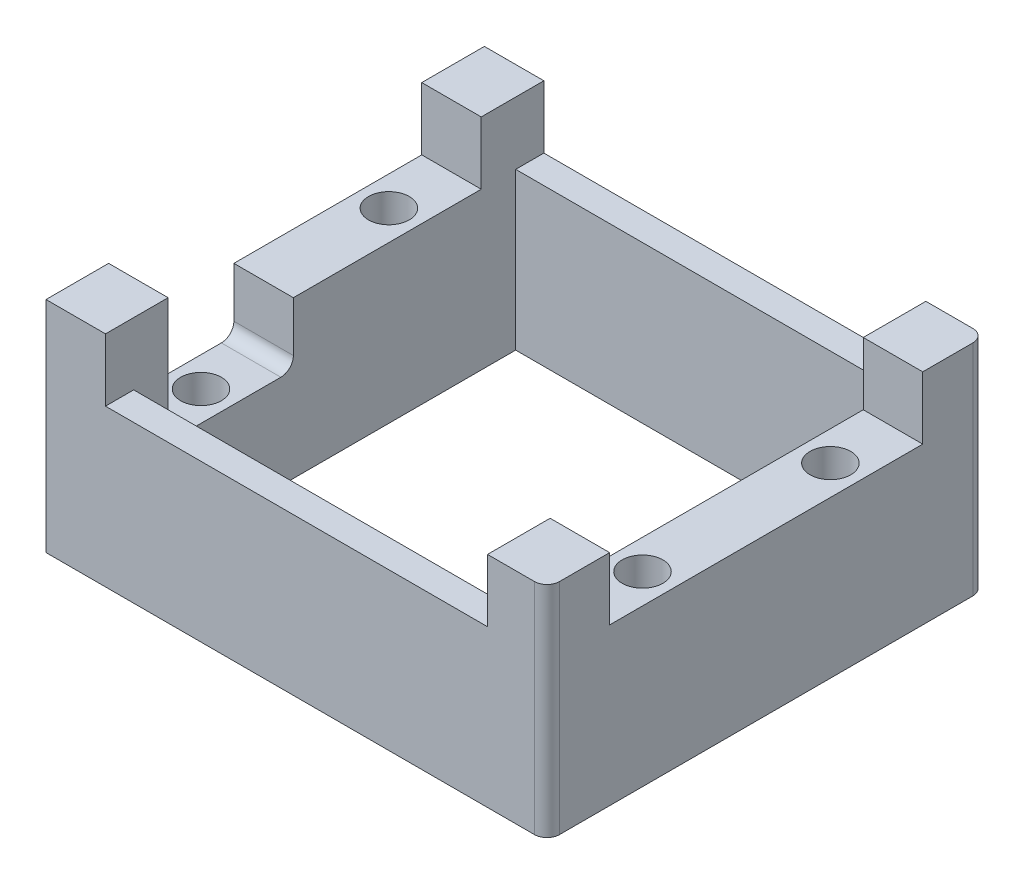
SolidWorks part; units mm, degrees
ref_plane "Front Plane" through (0, 0, 0) normal (0, 0, 1) x (1, 0, 0)
ref_plane "Top Plane" through (0, 0, 0) normal (0, 1, 0) x (1, 0, 0)
ref_plane "Right Plane" through (0, 0, 0) normal (1, 0, 0) x (0, 0, -1)
sketch "Sketch1" plane through (0, 0, 0) normal (0, 1, 0) x (1, 0, 0)
  line L1 (-35.2325, 39.1878) -> (44.7675, 39.1878)
  line L2 (-35.2325, 39.1878) -> (-35.2325, -30.8122)
  line L3 (-35.2325, -30.8122) -> (44.7675, -30.8122)
  line L4 (44.7675, 39.1878) -> (44.7675, -30.8122)
  dimension "D1" = 70
  dimension "D2" = 80
extrude "Boss-Extrude1" add sketch "Sketch1" along normal blind 25
sketch "Sketch2" plane through (0, 25, 0) normal (0, 1, 0) x (1, 0, 0)
  line L0 (-35.2325, 39.1878) -> (-35.2325, -30.8122) construction
  line L1 (-25.7325, 34.6878) -> (35.2675, 34.6878)
  line L2 (-25.7325, 34.6878) -> (-25.7325, -26.3122)
  line L3 (-25.7325, -26.3122) -> (35.2675, -26.3122)
  line L4 (35.2675, 34.6878) -> (35.2675, -26.3122)
  line L5 (44.7675, -30.8122) -> (44.7675, 39.1878) construction
  line L6 (44.7675, 39.1878) -> (-35.2325, 39.1878) construction
  line L7 (-35.2325, -30.8122) -> (44.7675, -30.8122) construction
  dimension "D1" = 9.5
  dimension "D2" = 9.5
  dimension "D3" = 4.5
  dimension "D4" = 4.5
extrude "Cut-Extrude1" cut sketch "Sketch2" against normal through all
sketch "Sketch3" plane through (0, 25, 0) normal (0, 1, 0) x (1, 0, 0)
  line L0 (-25.7325, 29.1878) -> (-35.2325, 29.1878)
  line L1 (-25.7325, 34.6878) -> (-25.7325, -26.3122) construction
  line L2 (-35.2325, 39.1878) -> (-35.2325, -30.8122) construction
  line L3 (-35.2325, 29.1878) -> (-35.2325, 39.1878)
  line L4 (-35.2325, 39.1878) -> (-25.7325, 39.1878)
  line L5 (44.7675, 39.1878) -> (-35.2325, 39.1878) construction
  line L6 (-25.7325, 29.1878) -> (-25.7325, 39.1878)
  line L8 (44.7675, 29.1878) -> (35.2675, 29.1878)
  line L10 (44.7675, -30.8122) -> (44.7675, 39.1878) construction
  line L11 (35.2675, -26.3122) -> (35.2675, 34.6878) construction
  line L12 (35.2675, 29.1878) -> (35.2675, 39.1878)
  line L13 (35.2675, 39.1878) -> (44.7675, 39.1878)
  line L14 (44.7675, 39.1878) -> (44.7675, 29.1878)
  line L15 (-25.7325, -20.8122) -> (-35.2325, -20.8122)
  line L16 (-35.2325, -20.8122) -> (-35.2325, -30.8122)
  line L17 (-35.2325, -30.8122) -> (-25.7325, -30.8122)
  line L18 (-35.2325, -30.8122) -> (44.7675, -30.8122) construction
  line L19 (-25.7325, -30.8122) -> (-25.7325, -20.8122)
  line L20 (35.2675, -20.8122) -> (44.7675, -20.8122)
  line L21 (44.7675, -20.8122) -> (44.7675, -30.8122)
  line L22 (44.7675, -30.8122) -> (35.2675, -30.8122)
  line L23 (35.2675, -30.8122) -> (35.2675, -20.8122)
  dimension "D1" = 10
  dimension "D2" = 9.5
  dimension "D3" = 10
extrude "Boss-Extrude2" add sketch "Sketch3" along normal blind 10
fillet "Fillet1" radius 2 1 edges at (44.7675, 17.5, 30.8122)
fillet "Fillet4" radius 2 1 edges at (44.7675, 17.5, -39.1878)
sketch "Sketch4" plane through (0, 25, 0) normal (0, 1, 0) x (1, 0, 0)
  line L0 (44.7675, -20.8122) -> (44.7675, 29.1878) construction
  line L3 (35.2675, 39.1878) -> (-25.7325, 39.1878) construction
  line L4 (-25.7325, -30.8122) -> (35.2675, -30.8122) construction
  point P0 (40.0175, 19.1878)
  point P1 (40.0175, -10.8122)
  point P9 (-30.4825, 19.1878)
  point P10 (-30.4825, -10.8122)
  dimension "D1" = 4.75
  dimension "D2" = 20
  dimension "D3" = 20
  dimension "D4" = 2
hole_wizard "CBORE for M3 SHCS1" positions "3DSketch1" profile "Sketch6" counterbore size "M3" standard "Ansi Metric" end condition through all
sketch3d "3DSketch1"
  point P0 (-30.4825, 25, -19.1878)
  point P3 (-30.4825, 25, 10.8122)
  point P6 (40.0175, 25, 10.8122)
  point P9 (40.0175, 25, -19.1878)
sketch "Sketch6" plane through (-30.4825, 25, -19.1878) normal (1, 0, 0) x (0, 0, 1)
  line L0 (0, 0) -> (0, 25)
  line L1 (0, 25) -> (1.7, 25)
  line L3 (1.7, 25) -> (1.7, 22)
  line L4 (1.7, 22) -> (3.25, 22)
  line L5 (3.25, 22) -> (3.25, 0)
  line L7 (3.25, 0) -> (0, 0)
  line L11 (0, -6.35) -> (0, 107.95) construction
  dimension "Thru Hole Dia." = 3.4
  dimension "Thru Hole Depth" = 25
  dimension "C'Bore Dia." = 6.5
  dimension "C'Bore Depth" = 22
sketch "Sketch7" plane through (-35.2325, 0, 0) normal (-1, 0, 0) x (0, 0, 1)
  line L0 (-29.1878, 25) -> (20.8122, 25) construction
  line L1 (30.8122, 35) -> (30.8122, 0) construction
  line L2 (-39.1878, 35) -> (-39.1878, 0) construction
  point P0 (25.8122, 20)
  point P5 (-34.1878, 20)
  dimension "D1" = 5
  dimension "D2" = 5
  dimension "D3" = 5
  dimension "D4" = 5
hole_wizard "Tap Drill for M3x0.5 Tap1" positions "3DSketch2" profile "Sketch8" hole size "M3x0.5" standard "Ansi Metric"
sketch3d "3DSketch2"
  point P0 (-35.2325, 20, 25.8122)
  point P3 (-35.2325, 20, -34.1878)
sketch "Sketch8" plane through (-35.2325, 20, 25.8122) normal (0, 1, 0) x (0, 0, 1)
  line L0 (0, 0) -> (0, 8.7511)
  line L1 (0, 8.7511) -> (1.25, 8)
  line L2 (1.25, 8) -> (1.25, 0)
  line L5 (1.25, 0) -> (0, 0)
  line L10 (0, 8.7511) -> (-1.25, 8) construction
  line L11 (0, -6.35) -> (0, 107.95) construction
  dimension "Hole Dia." = 2.5
  dimension "Hole Depth" = 8
  dimension "Drill Angle" = 118
sketch "Sketch9" plane through (-35.2325, 0, 0) normal (-1, 0, 0) x (0, 0, 1)
  line L1 (20.8122, 25) -> (0.8122, 25)
  line L2 (20.8122, 25) -> (20.8122, 15)
  line L3 (20.8122, 15) -> (0.8122, 15)
  line L4 (0.8122, 25) -> (0.8122, 15)
  dimension "D1" = 10
  dimension "D2" = 20
extrude "Cut-Extrude2" cut sketch "Sketch9" against normal up to next
fillet "Fillet5" radius 2 2 edges at (-30.4825, 15, 20.8122) (-30.4825, 15, 0.8122)
